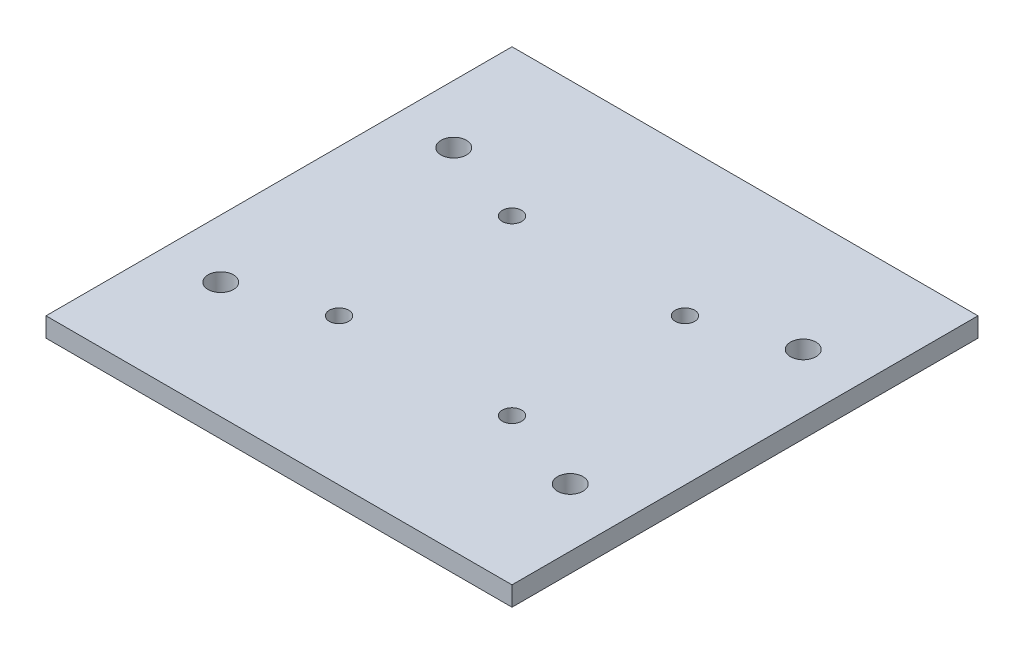
SolidWorks part; units mm, degrees
material "AISI 304"
ref_plane "Front Plane" through (0, 0, 0) normal (0, 0, 1) x (1, 0, 0)
ref_plane "Top Plane" through (0, 0, 0) normal (0, 1, 0) x (1, 0, 0)
ref_plane "Right Plane" through (0, 0, 0) normal (1, 0, 0) x (0, 0, -1)
sketch "Sketch1" plane through (0, 0, 0) normal (0, 1, 0) x (1, 0, 0)
  line L1 (0, 0) -> (152.4, 0)
  line L2 (0, 0) -> (0, 152.4)
  line L3 (0, 152.4) -> (152.4, 152.4)
  line L4 (152.4, 0) -> (152.4, 152.4)
  dimension "D1" = 152.4
  dimension "D2" = 152.4
extrude "Boss-Extrude1" add sketch "Sketch1" along normal blind 6.35 contours L3 L4 L1 L2
sketch "Sketch2" plane through (0, 6.35, 0) normal (0, 1, 0) x (1, 0, 0)
  line L0 (0, 0) -> (0, 152.4) construction
  line L1 (152.4, 0) -> (152.4, 152.4) construction
  line L2 (19.05, 152.4) -> (19.05, 0) construction
  line L3 (0, 152.4) -> (152.4, 152.4) construction
  line L4 (0, 0) -> (152.4, 0) construction
  line L5 (133.35, 152.4) -> (133.35, 0) construction
  line L6 (47.9157, 47.9157) -> (76.2, 76.2) construction
  line L7 (76.2, 76.2) -> (104.4843, 47.9157) construction
  line L8 (104.4843, 104.4843) -> (76.2, 76.2) construction
  line L9 (76.2, 76.2) -> (47.9157, 104.4843) construction
  line L10 (47.9157, 47.9157) -> (104.4843, 47.9157) construction
  line L16 (0, 171.45) -> (152.4, 171.45) construction
  line L17 (0, 171.45) -> (0, -19.05) construction
  line L18 (0, -19.05) -> (152.4, -19.05) construction
  line L19 (152.4, 171.45) -> (152.4, -19.05) construction
  circle A0 centre (19.05, 38.1) radius 4.1656
  circle A1 centre (19.05, 114.3) radius 4.1656
  circle A2 centre (133.35, 114.3) radius 4.1656
  circle A3 centre (133.35, 38.1) radius 4.1656
  circle A4 centre (104.4843, 104.4843) radius 3.175
  circle A5 centre (47.9157, 47.9157) radius 3.175
  circle A6 centre (47.9157, 104.4843) radius 3.175
  circle A7 centre (104.4843, 47.9157) radius 3.175
  circle A8 centre (76.2, 76.2) radius 40 construction
  point P34 (76.2, 0)
  point P35 (0, 76.2)
  point P36 (152.4, 76.2)
  dimension "D1" = 8.3312
  dimension "D2" = 8.3312
  dimension "D3" = 8.3312
  dimension "D4" = 8.3312
  dimension "D13" = 6.35
  dimension "D14" = 6.35
  dimension "D15" = 6.35
  dimension "D16" = 6.35
  dimension "D17" = 80
  dimension "D5" = 19.05
  dimension "D6" = 19.05
  dimension "D7" = 19.05
  dimension "D8" = 19.05
  dimension "D9" = 57.15
  dimension "D10" = 57.15
  dimension "D11" = 57.15
  dimension "D12" = 57.15
  dimension "D18" = 90
  dimension "D19" = 190.5
extrude "Cut-Extrude1" cut sketch "Sketch2" against normal through all both and the other way through all
sketch "Sketch3" plane through (0, 0, 0) normal (0, -1, 0) x (-1, 0, 0)
  circle A0 centre (-76.2, 76.2) radius 31.8782
